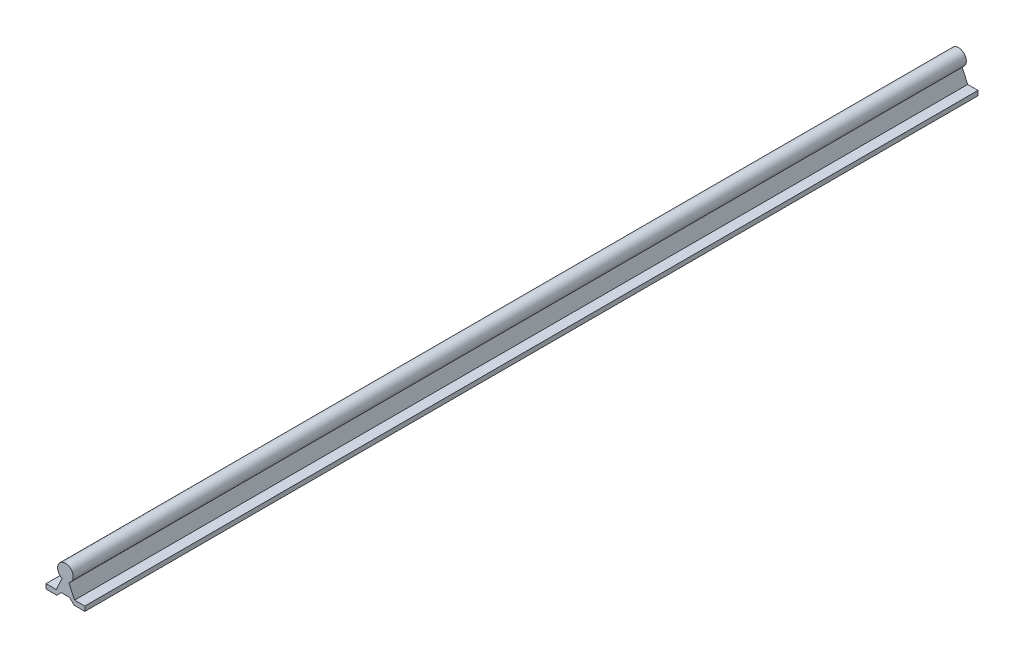
SolidWorks part; units mm, degrees
ref_plane "Front Plane" through (0, 0, 0) normal (0, 0, 1) x (1, 0, 0)
ref_plane "Top Plane" through (0, 0, 0) normal (0, 1, 0) x (1, 0, 0)
ref_plane "Right Plane" through (0, 0, 0) normal (1, 0, 0) x (0, 0, -1)
sketch "Sketch1" plane through (0, 0, 0) normal (0, 0, 1) x (1, 0, 0)
  line L0 (3.5, 17.6063) -> (9.375, 4.8)
  line L1 (19.875, 4.8) -> (9.375, 4.8)
  line L2 (19.875, 4.8) -> (19.875, 0)
  line L3 (19.875, 0) -> (8.875, 0)
  line L4 (-19.875, 4.8) -> (-19.875, 0)
  line L5 (19.875, 4.8) -> (-19.875, 0) construction
  line L6 (19.875, 0) -> (-19.875, 4.8) construction
  line L7 (-3.5, 17.6063) -> (-9.375, 4.8)
  line L8 (9.375, 4.8) -> (-9.375, 4.8) construction
  line L9 (-9.375, 4.8) -> (-19.875, 4.8)
  line L10 (-19.875, 0) -> (-8.875, 0)
  line L11 (-8.875, 0) -> (-4.275, 4.6)
  line L12 (-4.275, 4.6) -> (4.275, 4.6)
  line L13 (19.875, 0) -> (8.875, 0)
  line L14 (8.875, 0) -> (4.275, 4.6)
  line L15 (8.875, 0) -> (-8.875, 0) construction
  line L16 (-8.875, 0) -> (-19.875, 0)
  arc A0 (3.5, 17.6063) -> (-3.5, 17.6063) centre (0, 24.8) ccw
  arc A1 (-3.5, 17.6063) -> (3.5, 17.6063) centre (0, 24.8) ccw construction
  point P0 (0, 2.4)
  dimension "D1" = 16
  dimension "D2" = 24.8
  dimension "D3" = 39.75
  dimension "D4" = 4.8
  dimension "D5" = 7
  dimension "D6" = 18.75
  dimension "D7" = 4.6
  dimension "D8" = 11
  dimension "D9" = 11
  dimension "D10" = 45
extrude "Boss-Extrude1" add sketch "Sketch1" along normal blind 914.4 contours L0 A0 L7 L9 L4 L10 L11 L12 L14 L3 L2 L1
equation "\"length\"= 36in"
equation "\"D1@Boss-Extrude1\"=\"length\""
